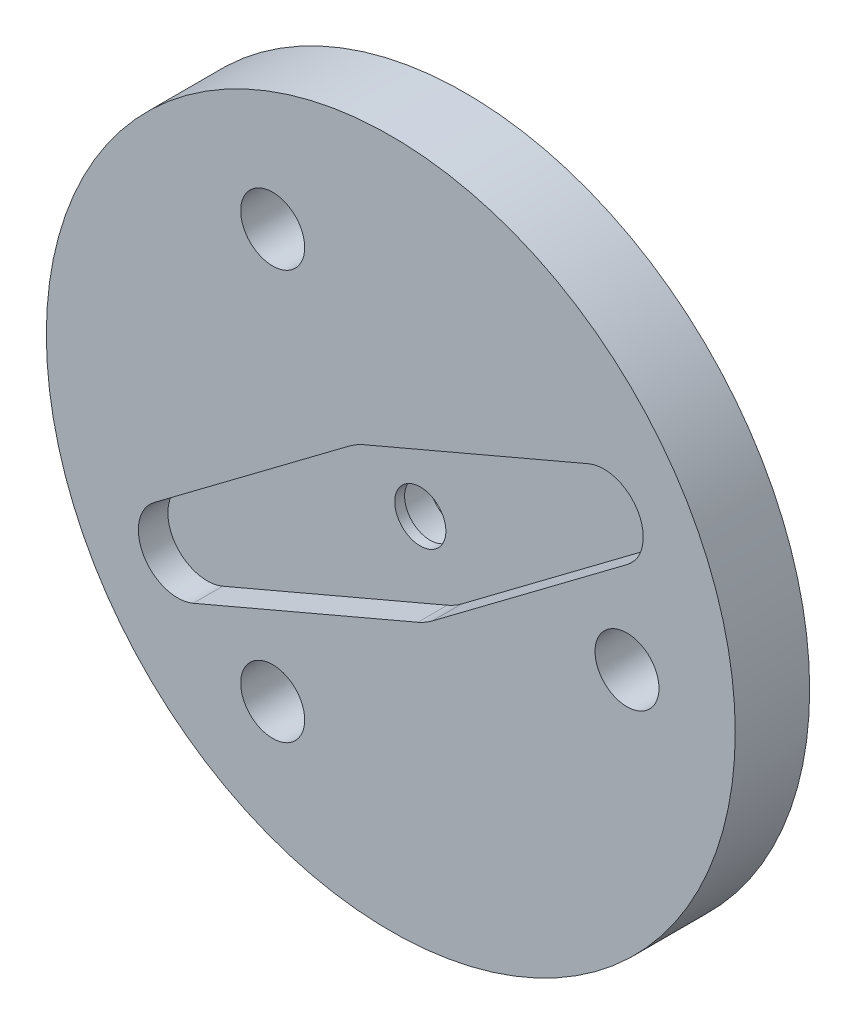
SolidWorks part; units mm, degrees
material "ABS PC"
ref_plane "Piano frontale" through (0, 0, 0) normal (0, 0, 1) x (1, 0, 0)
ref_plane "Piano superiore" through (0, 0, 0) normal (0, 1, 0) x (1, 0, 0)
ref_plane "Piano destro" through (0, 0, 0) normal (1, 0, 0) x (0, 0, -1)
sketch "Schizzo1" plane through (0, 0, 0) normal (0, 0, 1) x (1, 0, 0)
  circle A0 centre (0, 0) radius 17.5
  dimension "D1" = 35
extrude "Estrusione-Estrusione1" add sketch "Schizzo1" along normal blind 3.7811
sketch "Schizzo2" plane through (0, 0, 3.7811) normal (0, 0, 1) x (1, 0, 0)
  line L0 (12, 0) -> (0, 0)
  line L1 (0, 0) -> (-6.4084, 11.0997)
  line L2 (0, 0) -> (-6.3522, -11.0024)
  circle A0 centre (12, 0) radius 1.625
  circle A1 centre (-6, 10.3923) radius 1.625
  circle A2 centre (-6, -10.3923) radius 1.625
  circle A3 centre (0, 0) radius 1.3
  dimension "D1" = 3.25
  dimension "D9" = 2.6
  dimension "D2" = 12
  dimension "D3" = 120
  dimension "D4" = 120
  dimension "D6" = 12
  dimension "D8" = 12
extrude "Taglio-Estrusione1" cut sketch "Schizzo2" against normal through all
sketch "Schizzo3" plane through (0, 0, 3.7811) normal (0, 0, 1) x (1, 0, 0)
  line L0 (-1.133, 1.9625) -> (-6, 10.3923)
  line L1 (8.054, 4.65) -> (11.4619, 6.6175)
  line L3 (4.9966, 5.4828) -> (2.3247, 3.9694)
  line L4 (2.3247, 3.9694) -> (-7.2349, -1.579)
  line L5 (-4.9805, -5.4736) -> (7.2305, 1.5764)
  line L6 (-8.054, -4.65) -> (-11.1095, -6.4141)
  arc A0 (2.3247, 3.9694) -> (-4.5997, -0.0496) centre (0, 0) ccw
  arc A1 (7.2305, 1.5764) -> (4.9966, 5.4828) centre (6.1055, 3.525) ccw
  arc A3 (-7.2349, -1.579) -> (-4.9805, -5.4736) centre (-6.1055, -3.525) ccw
  arc A4 (-2.3496, -3.9546) -> (4.5996, 0.0575) centre (0, 0) ccw
  dimension "D1" = 9.2
  dimension "D2" = 4.5
  dimension "D4" = 4.5
  dimension "D3" = 7.05
  dimension "D5" = 7.05
sketch "Sketch1" plane through (0, 0, 3.7811) normal (0, 0, 1) x (1, 0, 0)
  line L4 (2.1011, -2.7992) -> (12.0259, 4.6505)
  line L5 (-10.0404, -8.0895) -> (1.3736, -3.2192)
  line L6 (-2.1011, 2.7992) -> (-12.0259, -4.6505)
  line L7 (10.0404, 8.0895) -> (-1.3736, 3.2192)
  line L8 (2.1011, -2.7992) -> (12.0259, 4.6505)
  line L9 (-10.0404, -8.0895) -> (1.3736, -3.2192)
  line L10 (-2.1011, 2.7992) -> (-12.0259, -4.6505)
  line L11 (10.0404, 8.0895) -> (-1.3736, 3.2192)
  arc A4 (1.3736, -3.2192) -> (2.1011, -2.7992) centre (0, 0) ccw
  arc A5 (-12.0259, -4.6505) -> (-10.0404, -8.0895) centre (-10.8253, -6.25) ccw
  arc A6 (-1.3736, 3.2192) -> (-2.1011, 2.7992) centre (0, 0) ccw
  arc A7 (12.0259, 4.6505) -> (10.0404, 8.0895) centre (10.8253, 6.25) ccw
  arc A8 (1.3736, -3.2192) -> (2.1011, -2.7992) centre (0, 0) ccw
  arc A9 (-12.0259, -4.6505) -> (-10.0404, -8.0895) centre (-10.8253, -6.25) ccw
  arc A10 (-1.3736, 3.2192) -> (-2.1011, 2.7992) centre (0, 0) ccw
  arc A11 (12.0259, 4.6505) -> (10.0404, 8.0895) centre (10.8253, 6.25) ccw
  dimension "D1" = 0
extrude "Cut-Extrude1" cut sketch "Sketch1" against normal blind 1.5
sketch "Schizzo4" plane through (0, 0, 0) normal (0, 0, -1) x (-1, 0, 0)
  circle A0 centre (0, 0) radius 2
extrude "Taglio-Estrusione2" cut sketch "Schizzo4" against normal offset from surface (1.7811 mm away) 0.5 up to face at (0, 0, 2.2811)
